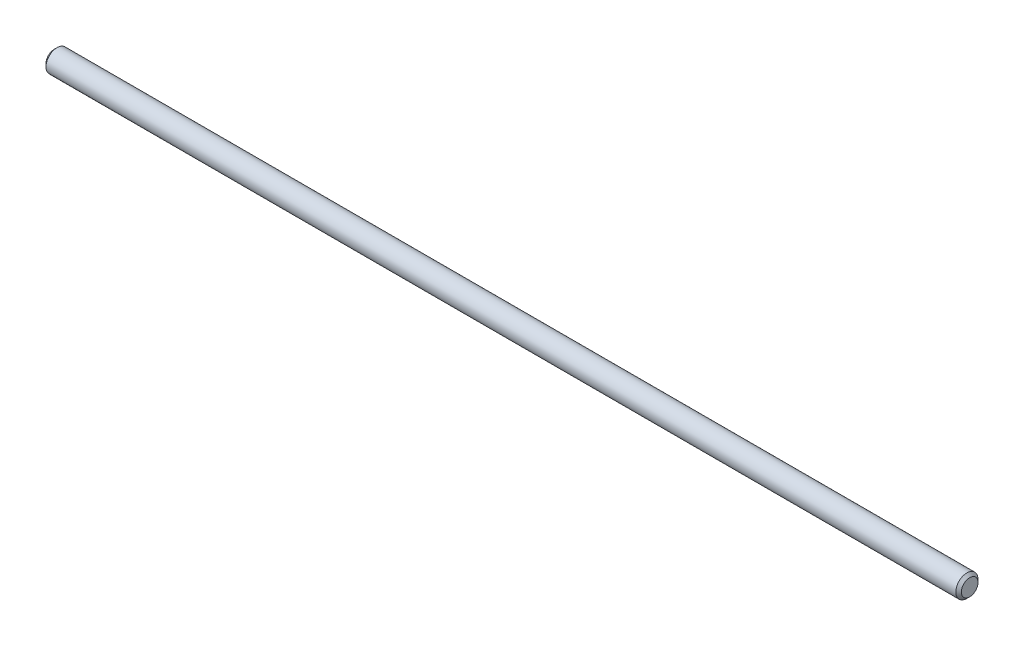
SolidWorks part; units mm, degrees
ref_plane "Alzado" through (0, 0, 0) normal (0, 0, 1) x (1, 0, 0)
ref_plane "Planta" through (0, 0, 0) normal (0, 1, 0) x (1, 0, 0)
ref_plane "Vista lateral" through (0, 0, 0) normal (1, 0, 0) x (0, 0, -1)
sketch "Croquis1" plane through (0, 0, 0) normal (1, 0, 0) x (0, 0, -1)
  circle A0 centre (0, 0) radius 4
  dimension "D1" = 8
extrude "Saliente-Extruir1" add sketch "Croquis1" along normal mid plane 330
chamfer "Chaflán1" distance 1 angle 45 2 edges at (-165, 0, -4) (165, 0, -4)
